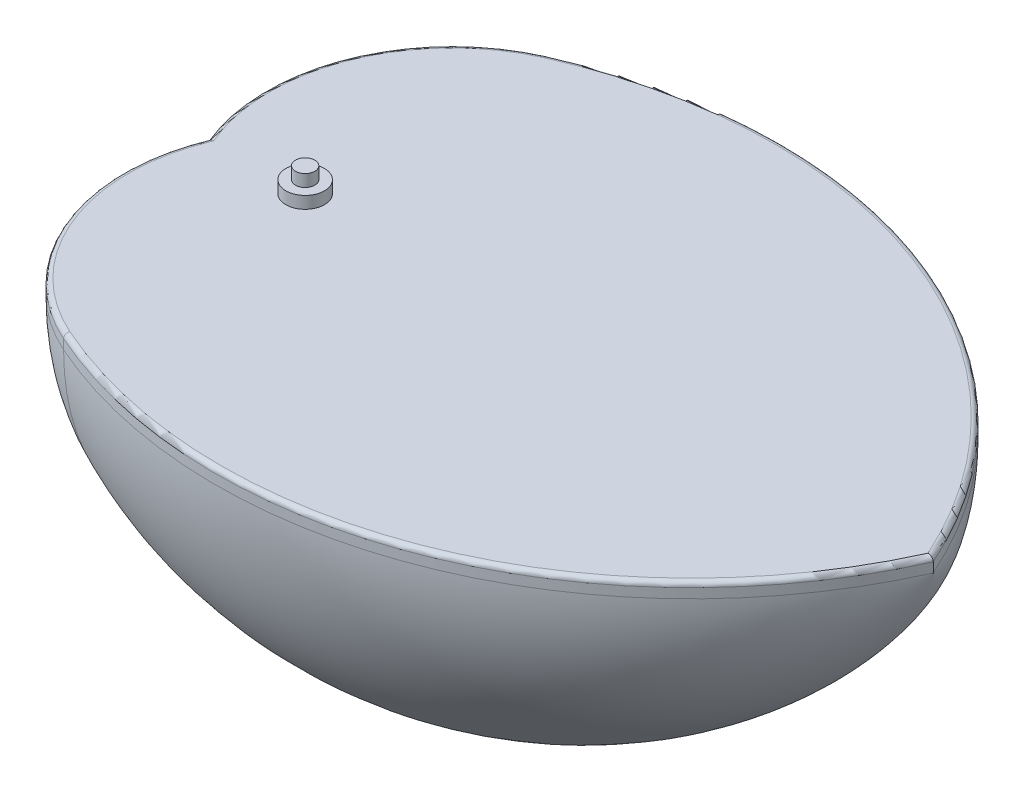
SolidWorks part; units mm, degrees
ref_plane "Front Plane" through (0, 0, 0) normal (0, 0, 1) x (1, 0, 0)
ref_plane "Top Plane" through (0, 0, 0) normal (0, 1, 0) x (1, 0, 0)
ref_plane "Right Plane" through (0, 0, 0) normal (1, 0, 0) x (0, 0, -1)
sketch "Sketch1" plane through (0, 0, 0) normal (0, 0, 1) x (1, 0, 0)
  line L0 (0, 0) -> (130, 50) construction
  line L1 (130, 50) -> (0, 50) construction
  line L2 (0, 50) -> (-20, 50) construction
  line L3 (-20, 50) -> (0, 0) construction
  line L4 (-17, 50) -> (0, 3) construction
  line L5 (0, 3) -> (127, 50) construction
  line L6 (0, 50) -> (0, 3) construction
  line L7 (0, 3) -> (0, 0) construction
  line L8 (-20, 50) -> (-17, 50)
  line L9 (127, 50) -> (130, 50)
  arc A0 (-20, 50) -> (0, 0) centre (15.6757, 35.2703) ccw
  arc A1 (0, 0) -> (130, 50) centre (40, 90) ccw
  arc A2 (-17, 50) -> (0, 3) centre (14.6553, 34.8753) ccw
  arc A3 (0, 3) -> (127, 50) centre (40, 90) ccw
  dimension "D1" = 150
  dimension "D2" = 50
  dimension "D3" = 20
  dimension "D4" = 3
  dimension "D5" = 3
  dimension "D6" = 3
revolve "Revolve1" add sketch "Sketch1" angle 180 mid plane about L2
sketch "Sketch2" plane through (0, 50, 0) normal (0, 1, 0) x (1, 0, 0)
  arc A0 (-20, 0) -> (0, -50) centre (15.6757, -14.7297) ccw construction
  arc A1 (0, -50) -> (130, 0) centre (40, 40) ccw construction
  arc A2 (130, 0) -> (0, 50) centre (40, -40) ccw construction
  arc A3 (0, 50) -> (-20, 0) centre (15.6757, 14.7297) ccw construction
  arc A4 (-20, 0) -> (0, -50) centre (15.6757, -14.7297) ccw
  arc A5 (0, -50) -> (130, 0) centre (40, 40) ccw
  arc A6 (130, 0) -> (0, 50) centre (40, -40) ccw
  arc A7 (0, 50) -> (-20, 0) centre (15.6757, 14.7297) ccw
extrude "Boss-Extrude1" add sketch "Sketch2" along normal blind 3
fillet "Fillet1" radius 1 4 edges at (75.3553, 53, -51.9239) (75.3553, 53, 51.9239) (-20.1606, 53, 29.0642) (-20.1606, 53, -29.0642)
sketch "Sketch4" plane through (0, 0, 0) normal (1, 0, 0) x (0, 0, -1)
  line L0 (0, 53) -> (0, 58)
  line L1 (0, 58) -> (2, 58)
  line L2 (2, 58) -> (2, 55.5)
  line L3 (2, 55.5) -> (4, 55.5)
  line L4 (4, 55.5) -> (4, 53)
  line L5 (57.4886, 53) -> (0, 53) construction
  line L6 (4, 53) -> (0, 53)
  dimension "D1" = 4
  dimension "D2" = 2.5
  dimension "D3" = 5
  dimension "D4" = 2
revolve "Revolve2" add sketch "Sketch4" angle 360 about L0
